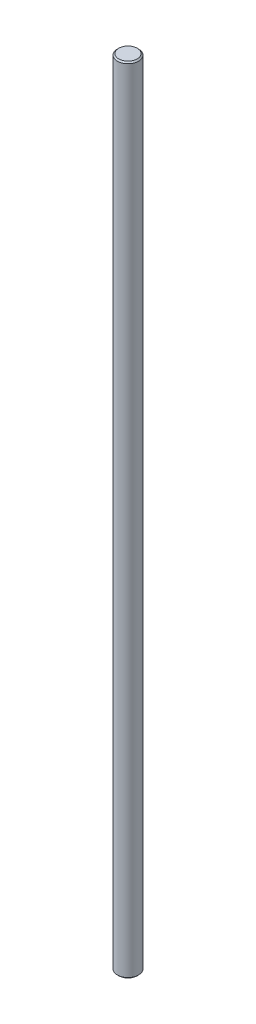
SolidWorks part; units mm, degrees
ref_plane "Front Plane" through (0, 0, 0) normal (0, 0, 1) x (1, 0, 0)
ref_plane "Top Plane" through (0, 0, 0) normal (0, 1, 0) x (1, 0, 0)
ref_plane "Right Plane" through (0, 0, 0) normal (1, 0, 0) x (0, 0, -1)
sketch "Sketch1" plane through (0, 0, 0) normal (0, 1, 0) x (1, 0, 0)
  circle A0 centre (0, 0) radius 4
  dimension "D1" = 8
extrude "Boss-Extrude1" add sketch "Sketch1" along normal blind 300
chamfer "Chamfer1" distance 0.5 angle 45 2 edges at (0, 0, 4) (0, 300, 4)
